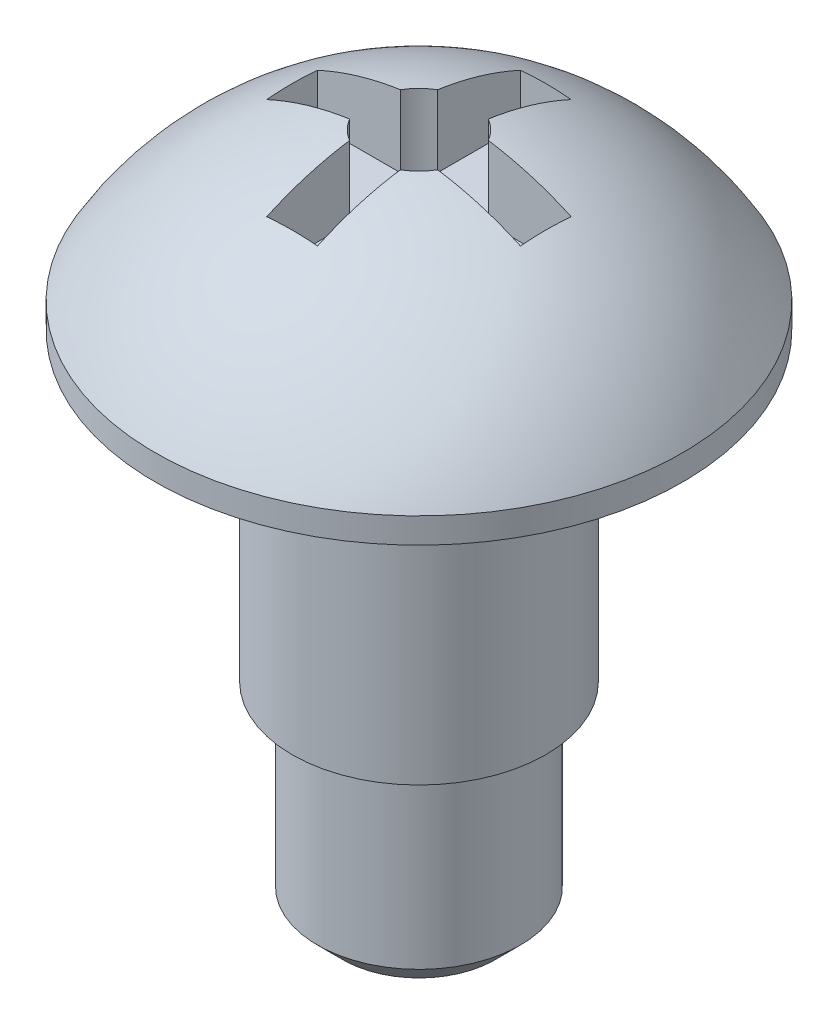
SolidWorks part; units mm, degrees
ref_plane "Plane1" through (0, 0, 0) normal (0, 0, 1) x (1, 0, 0)
ref_plane "Plane2" through (0, 0, 0) normal (0, 1, 0) x (1, 0, 0)
ref_plane "Plane3" through (0, 0, 0) normal (1, 0, 0) x (0, 0, -1)
sketch "Esquisse1" plane through (0, 0, 0) normal (0, 0, 1) x (1, 0, 0)
  line L0 (0, 0) -> (0, 26) construction
  line L2 (0, 3) -> (5.1962, 3)
  line L3 (0, 6) -> (0, 3)
  arc A0 (5.1962, 3) -> (0, 6) centre (0, 0) ccw
  dimension "D1" = 12
  dimension "D2" = 3
revolve "Base-Révolution" add sketch "Esquisse1" angle 360 about L0
sketch "Esquisse2" plane through (0, 3, 0) normal (0, -1, 0) x (1, 0, 0)
  circle A0 centre (0, 0) radius 5.1962
extrude "Boss.-Extru.1" add sketch "Esquisse2" along normal blind 0.5
sketch "Esquisse3" plane through (0, 2.5, 0) normal (0, -1, 0) x (1, 0, 0)
  circle A0 centre (0, 0) radius 2.5
  dimension "D1" = 5
extrude "Boss.-Extru.2" add sketch "Esquisse3" along normal blind 6
sketch "Esquisse4" plane through (0, -3.5, 0) normal (0, -1, 0) x (1, 0, 0)
  circle A0 centre (0, 0) radius 2
  dimension "D1" = 4
extrude "Boss.-Extru.3" add sketch "Esquisse4" along normal blind 4
chamfer "Chanfrein1" distance 0.5 angle 45
ref_plane "Plan1" through (0, 6.5, 0) normal (0, -1, 0) x (1, 0, 0)
sketch "Esquisse5" plane through (0, 6.5, 0) normal (0, -1, 0) x (1, 0, 0)
  line L0 (0, 0) -> (0, -3) construction
  line L1 (-0.5, -2.5) -> (-0.5, -0.866)
  line L2 (0.5, -2.5) -> (0.5, -0.866)
  line L3 (0.5, -2.5) -> (-0.5, -2.5)
  line L4 (-2.5, -0.5) -> (-2.5, 0.5)
  line L5 (-2.5, -0.5) -> (-0.866, -0.5)
  line L6 (-2.5, 0.5) -> (-0.866, 0.5)
  line L7 (-0.5, 2.5) -> (0.5, 2.5)
  line L8 (-0.5, 2.5) -> (-0.5, 0.866)
  line L9 (0.5, 2.5) -> (0.5, 0.866)
  line L10 (2.5, 0.5) -> (2.5, -0.5)
  line L11 (2.5, 0.5) -> (0.866, 0.5)
  line L12 (2.5, -0.5) -> (0.866, -0.5)
  arc A0 (-0.866, -0.5) -> (-0.5, -0.866) centre (0, 0) ccw
  arc A1 (0.5, -0.866) -> (0.866, -0.5) centre (0, 0) ccw
  arc A2 (0.866, 0.5) -> (0.5, 0.866) centre (0, 0) ccw
  arc A3 (-0.5, 0.866) -> (-0.866, 0.5) centre (0, 0) ccw
  dimension "D1" = 2
  dimension "D2" = 1
  dimension "D3" = 2.5
extrude "Enlèv. mat.-Extru.2" cut sketch "Esquisse5" along normal blind 2
